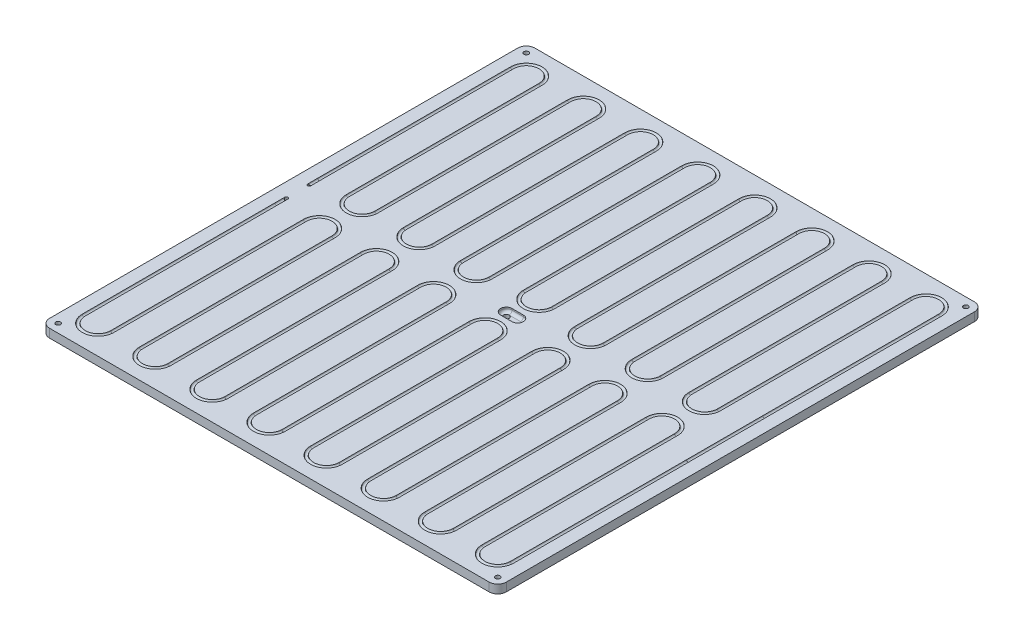
SolidWorks part; units mm, degrees
material "Клен"
ref_plane "Спереди" through (0, 0, 0) normal (0, 0, 1) x (1, 0, 0)
ref_plane "Сверху" through (0, 0, 0) normal (0, 1, 0) x (1, 0, 0)
ref_plane "Справа" through (0, 0, 0) normal (1, 0, 0) x (0, 0, -1)
sketch "Эскиз1" plane through (0, 0, 0) normal (0, 1, 0) x (1, 0, 0)
  line L0 (-199.4521, 0) -> (246.9406, 0) construction
  line L1 (-154, -156) -> (154, -156)
  line L2 (-160, -150) -> (-160, 178)
  line L3 (-154, 184) -> (154, 184)
  line L4 (160, -150) -> (160, 178)
  line L5 (-160, -160) -> (160, 160) construction
  line L6 (-160, 160) -> (160, -160) construction
  line L7 (0, -194.3379) -> (0, 187.7626) construction
  arc A0 (-154, -156) -> (-160, -150) centre (-154, -150) cw
  arc A1 (154, -156) -> (160, -150) centre (154, -150) ccw
  arc A2 (154, 184) -> (160, 178) centre (154, 178) cw
  arc A3 (-160, 178) -> (-154, 184) centre (-154, 178) cw
  point P0 (0, 0)
  dimension "D2" = 6
  dimension "D1" = 320
  dimension "D3" = 340
extrude "Бобышка-Вытянуть1" add sketch "Эскиз1" along normal blind 6
ref_plane "widht" through (0, 0, 0) normal (-1, 0, 0) x (0, 0, 1)
ref_plane "Плоскость2" through (0, 0, -14) normal (0, 0, -1) x (-1, 0, 0)
sketch "Эскиз2" plane through (0, 6, 0) normal (0, 1, 0) x (1, 0, 0)
  line L0 (-150, 29) -> (-150, 164)
  line L1 (-130, 29) -> (-130, 164)
  line L2 (176.8629, 19) -> (-212.1137, 19) construction
  line L3 (-187.9711, 174) -> (209.2971, 174) construction
  line L4 (-160, 178) -> (-160, -150) construction
  line L5 (-110, 29) -> (-110, 164)
  line L6 (-90, 29) -> (-90, 164)
  line L7 (-70, 29) -> (-70, 164)
  line L8 (-50, 29) -> (-50, 164)
  line L9 (-30, 29) -> (-30, 164)
  line L10 (-10, 33) -> (-10, 164)
  line L11 (10, 33) -> (10, 164)
  line L12 (30, 29) -> (30, 164)
  line L13 (50, 29) -> (50, 164)
  line L14 (70, 29) -> (70, 164)
  line L15 (90, 29) -> (90, 164)
  line L16 (110, 29) -> (110, 164)
  line L17 (130, 29) -> (130, 164)
  line L18 (150, 40.6471) -> (150, 164)
  line L19 (-150, 22) -> (-150, 29)
  line L20 (-15.4096, 23) -> (20, 23) construction
  line L21 (3.3, 14) -> (-3.3, 14) construction
  line L23 (-150, 6) -> (-150, -1)
  line L24 (150, -12.6471) -> (150, -136)
  line L25 (130, -1) -> (130, -136)
  line L26 (110, -1) -> (110, -136)
  line L27 (90, -1) -> (90, -136)
  line L28 (70, -1) -> (70, -136)
  line L29 (50, -1) -> (50, -136)
  line L30 (30, -1) -> (30, -136)
  line L31 (10, -5) -> (10, -136)
  line L32 (-10, -5) -> (-10, -136)
  line L33 (-30, -1) -> (-30, -136)
  line L34 (-50, -1) -> (-50, -136)
  line L35 (-70, -1) -> (-70, -136)
  line L36 (-90, -1) -> (-90, -136)
  line L37 (-110, -1) -> (-110, -136)
  line L38 (-130, -1) -> (-130, -136)
  line L39 (-150, -1) -> (-150, -136)
  line L40 (150, -12.6471) -> (150, 40.6471)
  line L41 (-221.0163, 22) -> (185.8343, 22) construction
  arc A0 (-150, 164) -> (-130, 164) centre (-140, 164) cw
  arc A1 (-110, 164) -> (-90, 164) centre (-100, 164) cw
  arc A2 (-70, 164) -> (-50, 164) centre (-60, 164) cw
  arc A3 (-30, 164) -> (-10, 164) centre (-20, 164) cw
  arc A4 (10, 164) -> (30, 164) centre (20, 164) cw
  arc A5 (50, 164) -> (70, 164) centre (60, 164) cw
  arc A6 (90, 164) -> (110, 164) centre (100, 164) cw
  arc A7 (130, 164) -> (150, 164) centre (140, 164) cw
  arc A8 (-130, 29) -> (-110, 29) centre (-120, 29) ccw
  arc A9 (-90, 29) -> (-70, 29) centre (-80, 29) ccw
  arc A10 (-50, 29) -> (-30, 29) centre (-40, 29) ccw
  arc A11 (-10, 33) -> (10, 33) centre (0, 33) ccw
  arc A12 (30, 29) -> (50, 29) centre (40, 29) ccw
  arc A13 (70, 29) -> (90, 29) centre (80, 29) ccw
  arc A14 (110, 29) -> (130, 29) centre (120, 29) ccw
  arc A15 (110, -1) -> (130, -1) centre (120, -1) cw
  arc A16 (70, -1) -> (90, -1) centre (80, -1) cw
  arc A17 (30, -1) -> (50, -1) centre (40, -1) cw
  arc A18 (-10, -5) -> (10, -5) centre (0, -5) cw
  arc A19 (-50, -1) -> (-30, -1) centre (-40, -1) cw
  arc A20 (-90, -1) -> (-70, -1) centre (-80, -1) cw
  arc A21 (-130, -1) -> (-110, -1) centre (-120, -1) cw
  arc A22 (130, -136) -> (150, -136) centre (140, -136) ccw
  arc A23 (90, -136) -> (110, -136) centre (100, -136) ccw
  arc A24 (50, -136) -> (70, -136) centre (60, -136) ccw
  arc A25 (10, -136) -> (30, -136) centre (20, -136) ccw
  arc A26 (-30, -136) -> (-10, -136) centre (-20, -136) ccw
  arc A27 (-70, -136) -> (-50, -136) centre (-60, -136) ccw
  arc A28 (-110, -136) -> (-90, -136) centre (-100, -136) ccw
  arc A29 (-150, -136) -> (-130, -136) centre (-140, -136) ccw
  point P0 (-150, 22)
  dimension "D2" = 20
  dimension "D5" = 10
  dimension "D4" = 8
  dimension "D6" = 20
  dimension "D8" = 20
  dimension "D9" = 20
  dimension "D10" = 20
  dimension "D11" = 20
  dimension "D12" = 20
  dimension "D13" = 20
  dimension "D14" = 20
  dimension "D15" = 20
  dimension "D16" = 20
  dimension "D17" = 20
  dimension "D18" = 20
  dimension "D19" = 20
  dimension "D20" = 20
  dimension "D3" = 5
  dimension "D7" = 9
ref_plane "Плоскость3" through (0, 0, -22) normal (0, 0, 1) x (1, 0, 0)
sketch "Эскиз3" plane through (0, 0, -22) normal (0, 0, 1) x (1, 0, 0)
  circle A1 centre (-150, 6) radius 1.1
  dimension "D1" = 2.2
sketch "Эскиз4" plane through (0, 6, 0) normal (0, 1, 0) x (1, 0, 0)
  line L0 (-4, 14) -> (4, 14) construction
  line L1 (3.3, 14) -> (-3.3, 14) construction
  line L2 (0, 3.3) -> (0, -3.3) construction
  line L3 (-4, 18) -> (4, 18)
  line L4 (-4, 10) -> (4, 10)
  arc A0 (-4, 18) -> (-4, 10) centre (-4, 14) ccw
  arc A1 (4, 10) -> (4, 18) centre (4, 14) ccw
  point P6 (0, 14)
  dimension "D1" = 8
  dimension "D2" = 8
extrude "Вырез-Вытянуть1" cut sketch "Эскиз4" against normal blind 3
fillet "Скругление4" radius 2 4 edges at (0, 3, -18) (8, 3, -14) (0, 3, -10) (-8, 3, -14)
sweep "Вырез-По траектории1" cut profiles "Эскиз3" path "Эскиз2"
sketch "Эскиз5" plane through (0, 6, 0) normal (0, 1, 0) x (1, 0, 0)
  line L0 (0, 3.3) -> (0, -3.3) construction
  line L1 (3.3, 14) -> (-3.3, 14) construction
  line L2 (-148.9, 22) -> (-151.1, 22) construction
  line L3 (-148.9, 6) -> (-151.1, 6) construction
  circle A0 centre (-154, 178) radius 1.65
  circle A1 centre (154, 178) radius 1.65
  circle A2 centre (154, -150) radius 1.65
  circle A3 centre (-154, -150) radius 1.65
  circle A5 centre (-4, 14) radius 2
  circle A6 centre (-150, 22) radius 1.102
  circle A7 centre (-150, 6) radius 1.1033
  point P0 (-154, 178)
  point P14 (-4, 14)
  dimension "D1" = 3.3
  dimension "D2" = 4
extrude "Вырез-Вытянуть2" cut sketch "Эскиз5" against normal through all
equation "\"D6@Эскиз2\"=\"D2@Эскиз2\""
equation "\"D8@Эскиз2\"=\"D2@Эскиз2\""
equation "\"D9@Эскиз2\"=\"D2@Эскиз2\""
equation "\"D11@Эскиз2\"=\"D2@Эскиз2\""
equation "\"D12@Эскиз2\"=\"D2@Эскиз2\""
equation "\"D13@Эскиз2\"=\"D2@Эскиз2\""
equation "\"D14@Эскиз2\"=\"D2@Эскиз2\""
equation "\"D15@Эскиз2\"=\"D2@Эскиз2\""
equation "\"D16@Эскиз2\"=\"D2@Эскиз2\""
equation "\"D17@Эскиз2\"=\"D2@Эскиз2\""
equation "\"D18@Эскиз2\"=\"D2@Эскиз2\""
equation "\"D20@Эскиз2\"=\"D2@Эскиз2\""
equation "\"D7@Эскиз2\"=\"D3@Эскиз2\"+4"
